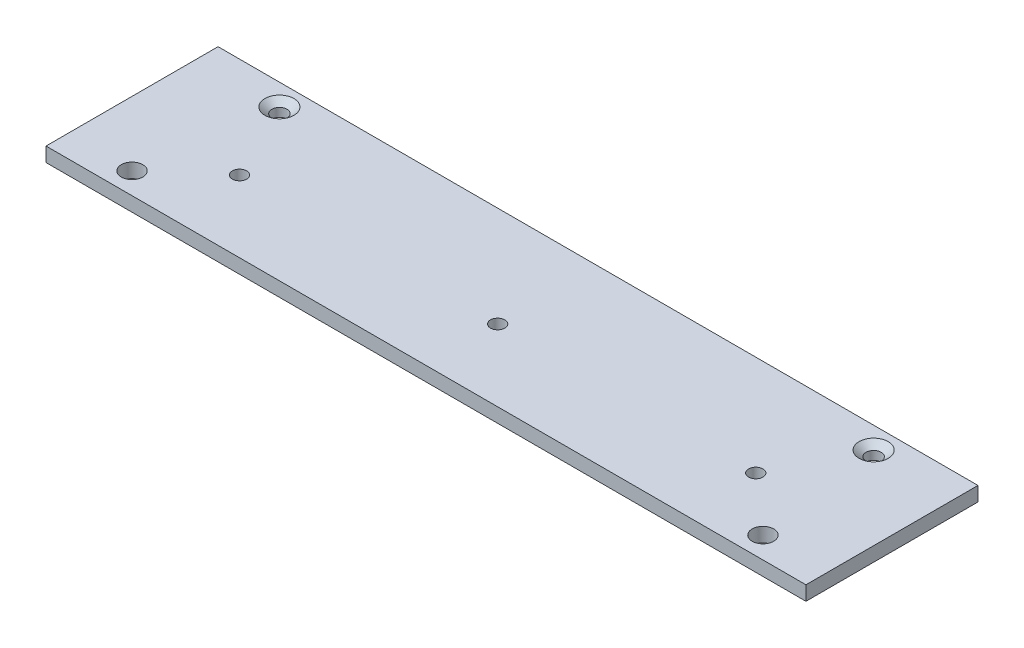
SolidWorks part; units mm, degrees
material "6061-T6 (SS)"
ref_plane "Front Plane" through (0, 0, 0) normal (0, 0, 1) x (1, 0, 0)
ref_plane "Top Plane" through (0, 0, 0) normal (0, 1, 0) x (1, 0, 0)
ref_plane "Right Plane" through (0, 0, 0) normal (1, 0, 0) x (0, 0, -1)
sketch "Sketch1" plane through (0, 0, 0) normal (0, 1, 0) x (1, 0, 0)
  line L0 (0, 94.0594) -> (0, -114.8103) construction
  line L1 (-168.275, 50.8) -> (168.275, 50.8)
  line L2 (-168.275, 50.8) -> (-168.275, -25.4)
  line L3 (-168.275, -25.4) -> (168.275, -25.4)
  line L4 (168.275, 50.8) -> (168.275, -25.4)
  circle A0 centre (-139.7, -15.875) radius 4.7625
  circle A1 centre (139.7, -15.875) radius 4.7625
  circle A2 centre (131.572, 41.275) radius 3.175
  circle A3 centre (-131.572, 41.275) radius 3.175
  point P0 (0, 0)
  point P21 (0, 50.8)
  dimension "D4" = 9.525
  dimension "D6" = 6.35
  dimension "D7" = 6.35
  dimension "D1" = 336.55
  dimension "D2" = 76.2
  dimension "D3" = 279.4
  dimension "D5" = 9.525
  dimension "D8" = 50.8
extrude "Boss-Extrude1" add sketch "Sketch1" along normal mid plane 6.35
hole_wizard "CSK for 1/4 Flat Head Machine Screw (100)1" positions "Sketch2" profile "Sketch3" countersink size "1/4" standard "ANSI Inch" end condition through all
sketch "Sketch2" plane through (0, 3.175, 0) normal (0, 1, 0) x (1, 0, 0)
  point P0 (-131.572, 41.275)
  point P3 (131.572, 41.275)
sketch "Sketch3" plane through (-131.572, 3.175, -41.275) normal (1, 0, 0) x (0, 0, 1)
  line L0 (0, 0) -> (0, 6.35)
  line L1 (0, 6.35) -> (3.3782, 6.35)
  line L2 (3.3782, 6.35) -> (3.3782, 2.5682)
  line L3 (3.3782, 2.5682) -> (6.4389, 0)
  line L5 (6.4389, 0) -> (0, 0)
  line L6 (-3.3782, 2.5682) -> (-6.4389, 0) construction
  line L11 (0, -6.35) -> (0, 107.95) construction
  dimension "Thru Hole Dia." = 6.7564
  dimension "Thru Hole Depth" = 6.35
  dimension "Near C'Sink Dia." = 12.8778
  dimension "Near C'Sink Angle" = 100
sketch "Sketch4" [suppressed] plane through (0, 3.175, 0) normal (0, 1, 0) x (1, 0, 0)
  line L0 (168.275, 50.8) -> (-168.275, 50.8) construction
  circle A0 centre (0, 41.275) radius 2.7781
  dimension "D2" = 5.5562
  dimension "D1" = 9.525
extrude "Cut-Extrude1" [suppressed] cut sketch "Sketch4" against normal through all both and the other way through all
sketch "Sketch5" plane through (0, 3.175, 0) normal (0, 1, 0) x (1, 0, 0)
  line L0 (0, -62.9837) -> (0, 72.9322) construction
  line L1 (-168.275, -25.4) -> (168.275, -25.4) construction
  circle A0 centre (-114.3, 6.35) radius 3.175
  circle A1 centre (114.3, 6.35) radius 3.175
  circle A3 centre (0, 6.35) radius 3.175
  point P5 (0, 0)
  point P8 (0, 0)
  dimension "D1" = 6.35
  dimension "D2" = 228.6
  dimension "D3" = 31.75
extrude "Cut-Extrude2" cut sketch "Sketch5" against normal through all both and the other way through all
